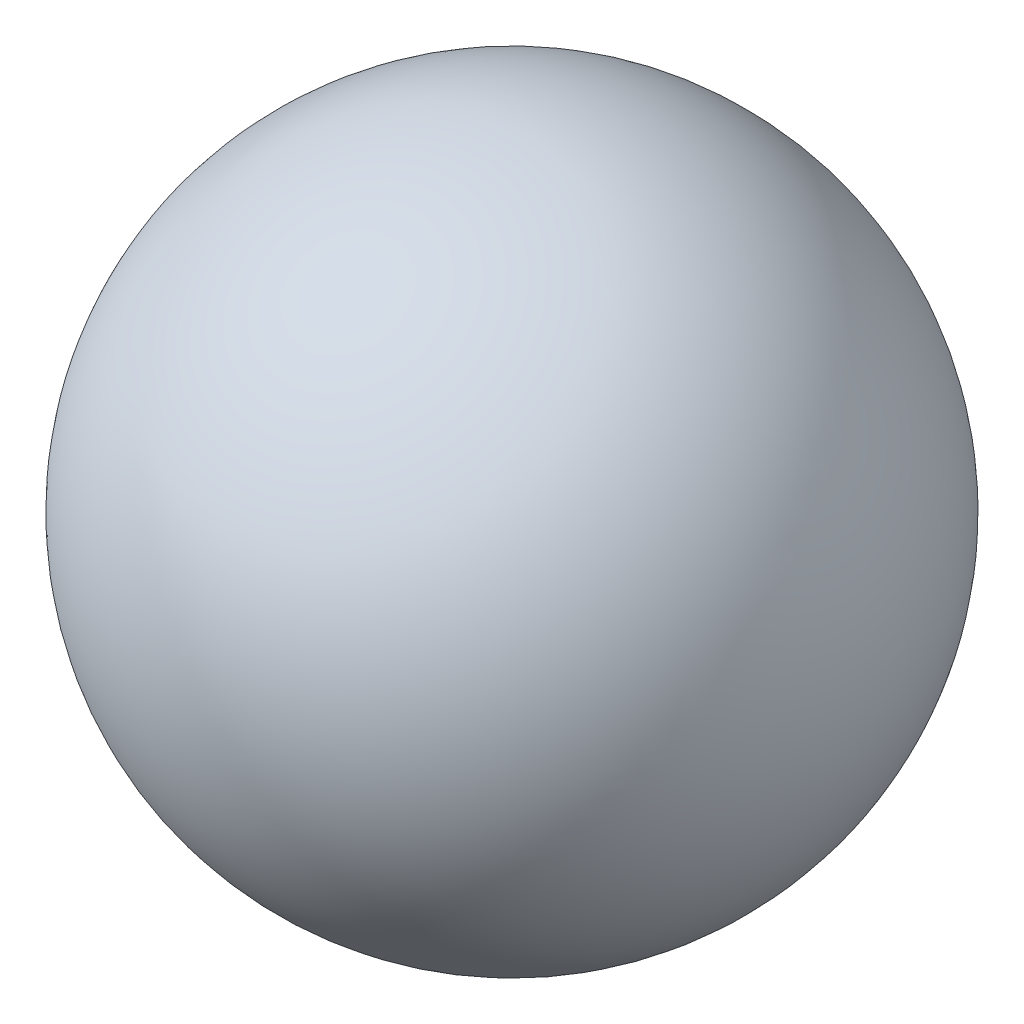
SolidWorks part; units mm, degrees
material "Cast Stainless Steel"
ref_plane "Front Plane" through (0, 0, 0) normal (0, 0, 1) x (1, 0, 0)
ref_plane "Top Plane" through (0, 0, 0) normal (0, 1, 0) x (1, 0, 0)
ref_plane "Right Plane" through (0, 0, 0) normal (1, 0, 0) x (0, 0, -1)
sketch "Sketch1" plane through (0, 0, 0) normal (0, 0, 1) x (1, 0, 0)
  line L0 (-12, 0) -> (12, 0)
  arc A0 (12, 0) -> (-12, 0) centre (0, 0) cw
  dimension "D1" = 24
revolve "Revolve1" add sketch "Sketch1" angle 360 about L0
